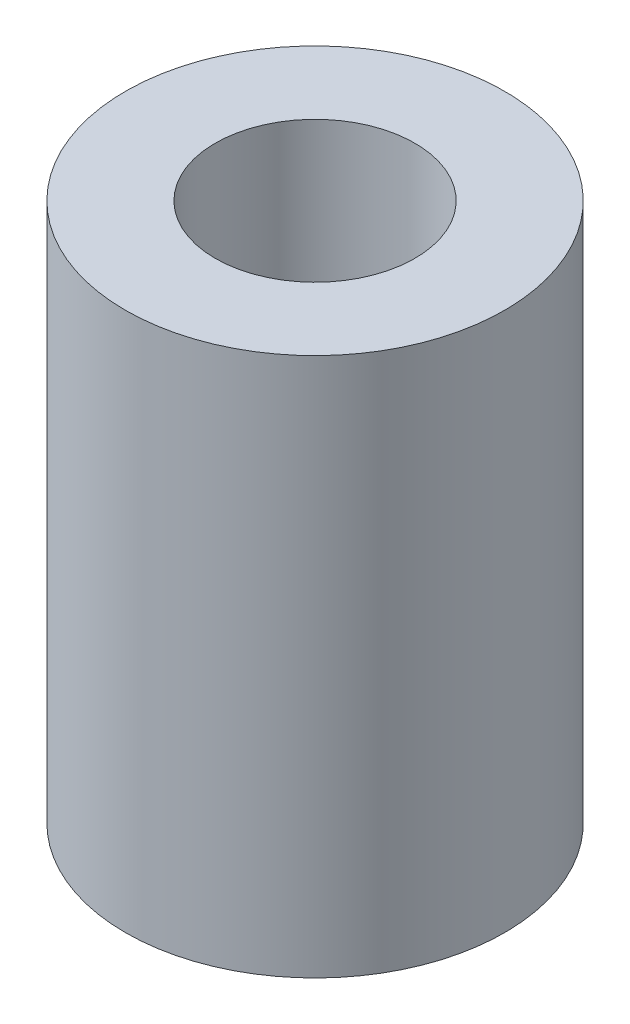
SolidWorks part; units mm, degrees
ref_plane "Front Plane" through (0, 0, 0) normal (0, 0, 1) x (1, 0, 0)
ref_plane "Top Plane" through (0, 0, 0) normal (0, 1, 0) x (1, 0, 0)
ref_plane "Right Plane" through (0, 0, 0) normal (1, 0, 0) x (0, 0, -1)
sketch "Sketch1" plane through (0, 0, 0) normal (0, 1, 0) x (1, 0, 0)
  circle A0 centre (0, 0) radius 4.75
  dimension "D1" = 9.5
extrude "Boss-Extrude1" add sketch "Sketch1" along normal blind 13.5
sketch "Sketch2" plane through (0, 13.5, 0) normal (0, 1, 0) x (1, 0, 0)
  circle A0 centre (0, 0) radius 2.5
  dimension "D1" = 5
extrude "Cut-Extrude1" cut sketch "Sketch2" against normal blind 7
